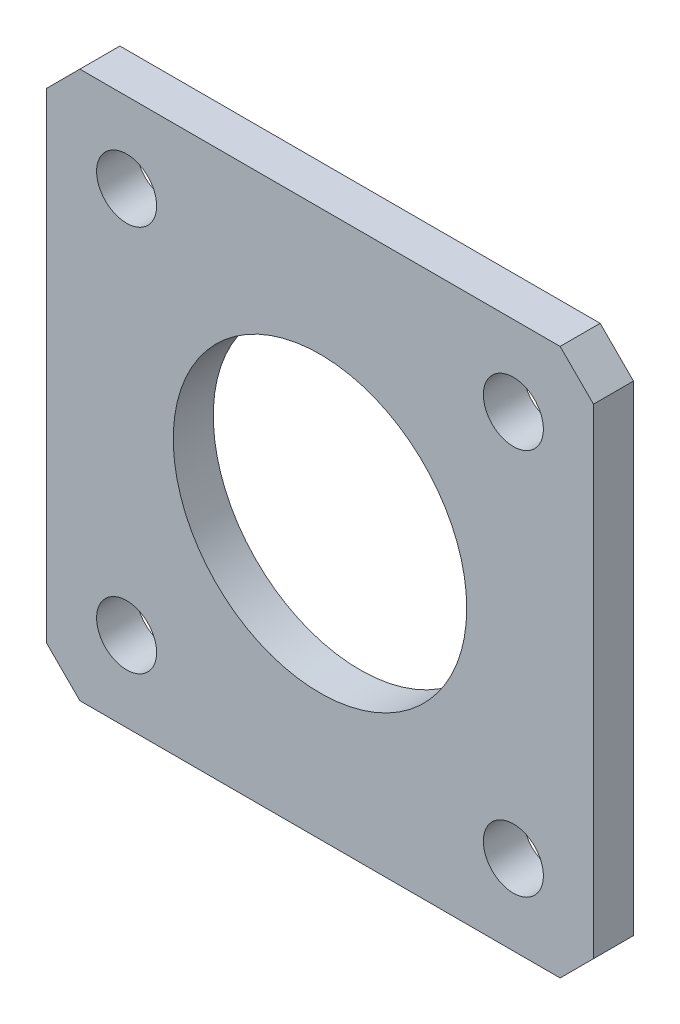
SolidWorks part; units mm, degrees
material "Ст 3 ГОСТ 380-2005"
ref_plane "Спереди" through (0, 0, 0) normal (0, 0, 1) x (1, 0, 0)
ref_plane "Сверху" through (0, 0, 0) normal (0, 1, 0) x (1, 0, 0)
ref_plane "Слева" through (0, 0, 0) normal (1, 0, 0) x (0, 0, -1)
sketch "Эскиз1" plane through (0, 0, 0) normal (0, 0, 1) x (1, 0, 0)
  line L1 (-20.5, -20.5) -> (20.5, -20.5)
  line L2 (-20.5, -20.5) -> (-20.5, 20.5)
  line L3 (-20.5, 20.5) -> (20.5, 20.5)
  line L4 (20.5, -20.5) -> (20.5, 20.5)
  line L5 (-20.5, -20.5) -> (20.5, 20.5) construction
  line L6 (-20.5, 20.5) -> (20.5, -20.5) construction
  circle A0 centre (0, 0) radius 11
  point P0 (0, 0)
  dimension "D2" = 22
  dimension "D1" = 41
extrude "Вытянуть1" add sketch "Эскиз1" along normal blind 3
sketch "Эскиз4" plane through (0, 0, 3) normal (0, 0, 1) x (1, 0, 0)
  line L0 (-20.5, 20.5) -> (20.5, -20.5) construction
  line L1 (20.5, 20.5) -> (-20.5, -20.5) construction
  circle A0 centre (0, 0) radius 20.5 construction
  circle A1 centre (-14.4957, 14.4957) radius 2.25
  circle A2 centre (14.4957, 14.4957) radius 2.25
  circle A3 centre (14.4957, -14.4957) radius 2.25
  circle A4 centre (-14.4957, -14.4957) radius 2.25
  circle A5 centre (0, 0) radius 15 construction
  dimension "D1" = 41
  dimension "D2" = 4.5
  dimension "D3" = 30
extrude "Вытянуть2" cut sketch "Эскиз4" against normal through all
chamfer "Фаска1" distance 2.5 angle 45 4 edges at (-20.5, 20.5, 1.5) (20.5, 20.5, 1.5) (20.5, -20.5, 1.5) (-20.5, -20.5, 1.5)
